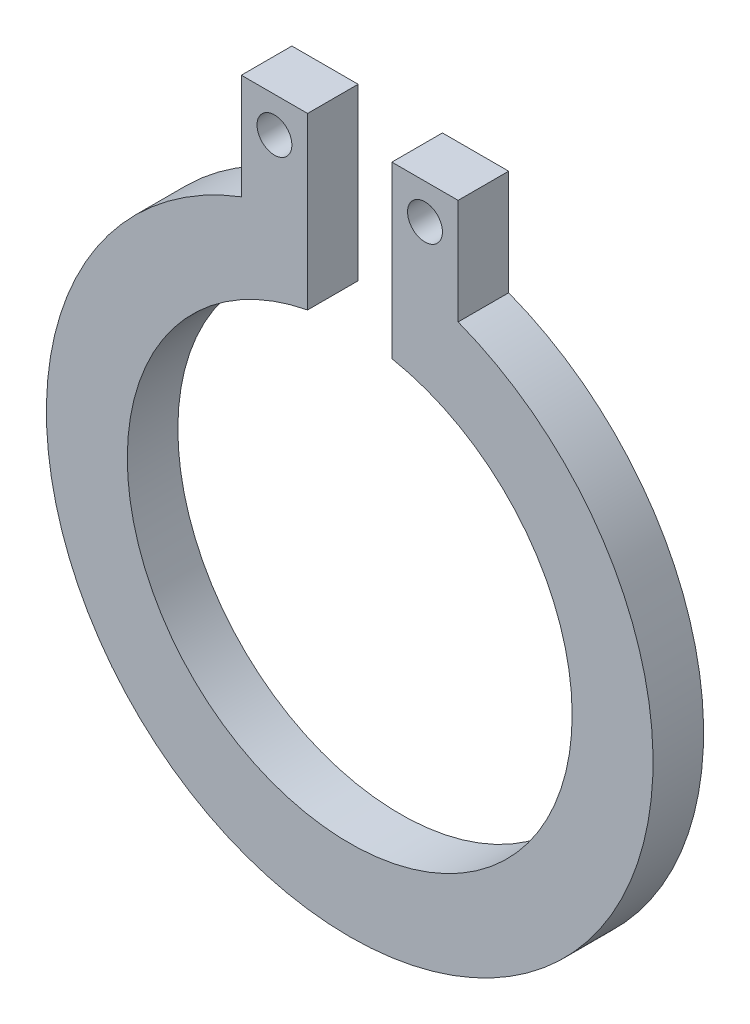
SolidWorks part; units mm, degrees
ref_plane "Płaszczyzna przednia" through (0, 0, 0) normal (0, 0, 1) x (1, 0, 0)
ref_plane "Płaszczyzna górna" through (0, 0, 0) normal (0, 1, 0) x (1, 0, 0)
ref_plane "Płaszczyzna prawa" through (0, 0, 0) normal (1, 0, 0) x (0, 0, -1)
sketch "Szkic1" plane through (0, 0, 0) normal (0, 0, 1) x (1, 0, 0)
  line L0 (1.072, 2.8019) -> (1.072, 3.8437)
  line L1 (0, 0) -> (0, 4.6571) construction
  line L2 (1.072, 3.8437) -> (0.4168, 3.8437)
  line L3 (0.4168, 3.8437) -> (0.4168, 2.1602)
  line L4 (-1.072, 2.8019) -> (-1.072, 3.8437)
  line L5 (-1.072, 3.8437) -> (-0.4168, 3.8437)
  line L6 (-0.4168, 3.8437) -> (-0.4168, 2.1602)
  arc A0 (-0.4168, 2.1602) -> (0.4168, 2.1602) centre (0, 0) ccw
  arc A1 (-1.072, 2.8019) -> (1.072, 2.8019) centre (0, 0) ccw
  circle A2 centre (0.7444, 3.4952) radius 0.1724
  circle A3 centre (-0.7444, 3.4952) radius 0.1724
  dimension "D1" = 4.4
  dimension "D2" = 6
extrude "Dodanie-wyciągnięcie1" add sketch "Szkic1" along normal blind 0.5
